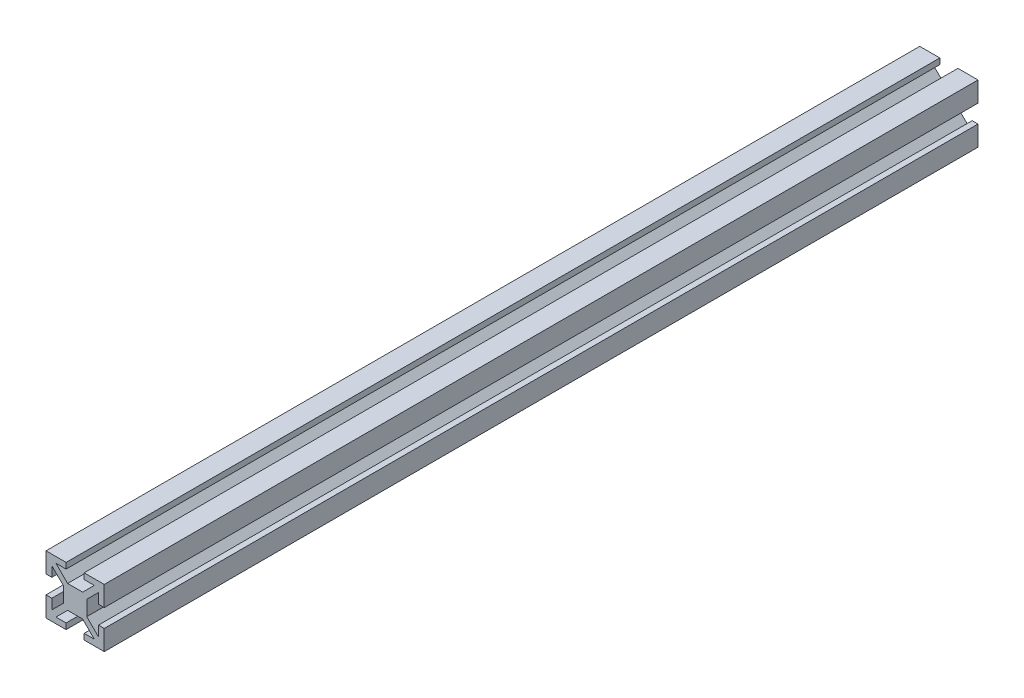
SolidWorks part; units mm, degrees
material "1060 Alloy"
ref_plane "Front Plane" through (0, 0, 0) normal (0, 0, 1) x (1, 0, 0)
ref_plane "Top Plane" through (0, 0, 0) normal (0, 1, 0) x (1, 0, 0)
ref_plane "Right Plane" through (0, 0, 0) normal (1, 0, 0) x (0, 0, -1)
sketch "Sketch1" plane through (0, 0, 0) normal (0, 0, 1) x (1, 0, 0)
  line L0 (-8, 6.5858) -> (-4, 2.5858)
  line L1 (-10, -10) -> (-3.1, -10)
  line L2 (-10, -10) -> (-10, -3.1)
  line L3 (-10, 10) -> (-3.1, 10)
  line L4 (10, -10) -> (10, -3.1)
  line L5 (-10, -10) -> (10, 10) construction
  line L6 (-10, 10) -> (10, -10) construction
  line L7 (-6.5858, -8) -> (-3.1, -8)
  line L8 (-8, -6.5858) -> (-8, -3.1)
  line L9 (-6.5858, 8) -> (-3.1, 8)
  line L10 (8, -6.5858) -> (8, -3.1)
  line L11 (-8, 3.1) -> (-8, -3.1) construction
  line L13 (-2.5858, -4) -> (2.5858, -4)
  line L14 (-4, -2.5858) -> (-4, 2.5858)
  line L15 (-2.5858, 4) -> (2.5858, 4)
  line L16 (4, -2.5858) -> (4, 2.5858)
  line L19 (-6.5858, 8) -> (-2.5858, 4)
  line L20 (6.5858, 8) -> (2.5858, 4)
  line L21 (8, 6.5858) -> (4, 2.5858)
  line L22 (8, -6.5858) -> (4, -2.5858)
  line L23 (6.5858, -8) -> (2.5858, -4)
  line L24 (-6.5858, -8) -> (-2.5858, -4)
  line L25 (-8, -6.5858) -> (-4, -2.5858)
  line L26 (-3.1, 10) -> (-3.1, 8)
  line L27 (3.1, 10) -> (3.1, 8)
  line L29 (10, 3.1) -> (8, 3.1)
  line L30 (10, -3.1) -> (8, -3.1)
  line L31 (3.1, -10) -> (3.1, -8)
  line L32 (-3.1, -10) -> (-3.1, -8)
  line L33 (-10, -3.1) -> (-8, -3.1)
  line L34 (-10, 3.1) -> (-8, 3.1)
  line L35 (-8, 3.1) -> (-8, 6.5858)
  line L36 (-10, 3.1) -> (-10, 10)
  line L37 (3.1, -8) -> (6.5858, -8)
  line L38 (3.1, 8) -> (6.5858, 8)
  line L39 (3.1, 10) -> (10, 10)
  line L40 (3.1, -10) -> (10, -10)
  line L41 (8, 3.1) -> (8, 6.5858)
  line L42 (10, 3.1) -> (10, 10)
  point P0 (0, 0)
  point P6 (0, 0)
  point P8 (-8, 0)
  point P35 (0, 0)
  point P54 (0, 0)
  dimension "D1" = 20
  dimension "D2" = 2
  dimension "D3" = 6
  dimension "D4" = 2
  dimension "D6" = 6.2
  dimension "D5" = 4
  dimension "D7" = 4
extrude "Boss-Extrude1" add sketch "Sketch1" along normal blind 300
sketch "Sketch2" plane through (-4, 0, 0) normal (-1, 0, 0) x (0, 0, 1)
  circle A0 centre (150, 0) radius 2.6
  dimension "D1" = 5.2
extrude "Cut-Extrude1" cut sketch "Sketch2" against normal through all
